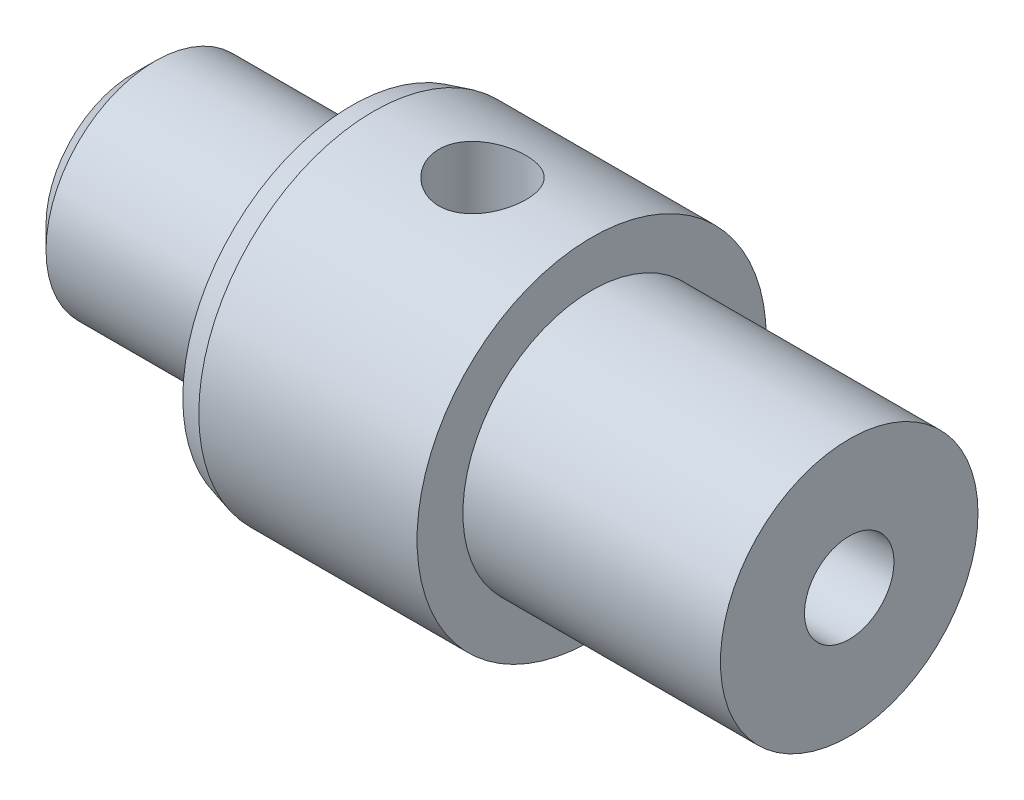
SolidWorks part; units mm, degrees
ref_plane "Front Plane" through (0, 0, 0) normal (0, 0, 1) x (1, 0, 0)
ref_plane "Top Plane" through (0, 0, 0) normal (0, 1, 0) x (1, 0, 0)
ref_plane "Right Plane" through (0, 0, 0) normal (1, 0, 0) x (0, 0, -1)
sketch "Sketch1" plane through (0, 0, 0) normal (0, 0, 1) x (1, 0, 0)
  line L0 (5, 4) -> (5, 0)
  line L1 (5, 0) -> (10.5, 0)
  line L2 (10.5, 0) -> (10.5, 4)
  line L3 (10.5, 4) -> (5, 4)
  line L4 (5, 0) -> (10.5, 0) construction
revolve "Revolve1" add sketch "Sketch1" angle 360 about L4
sketch "Sketch2" plane through (5, 0, 0) normal (-1, 0, 0) x (0, 0, 1)
  circle A0 centre (0, 0) radius 2.5
extrude "Boss-Extrude1" add sketch "Sketch2" along normal blind 5
sketch "Sketch3" plane through (10.5, 0, 0) normal (1, 0, 0) x (0, 0, -1)
  circle A0 centre (0, 0) radius 2.95
extrude "Boss-Extrude2" add sketch "Sketch3" along normal blind 5.9
hole_wizard "Ø2.0 (2) Diameter Hole1" positions "3DSketch1" profile "Sketch4" hole size "Ø2.0" standard "ANSI Metric"
sketch3d "3DSketch1"
  point P0 (8, -4, 0)
sketch "Sketch4" plane through (8, -4, 0) normal (1, 0, 0) x (0, 0, -1)
  line L0 (0, 0) -> (0, 8)
  line L1 (0, 8) -> (1, 8)
  line L2 (1, 8) -> (1, 0)
  line L5 (1, 0) -> (0, 0)
  line L11 (0, -6.35) -> (0, 107.95) construction
  dimension "Thru Hole Dia." = 2
  dimension "Thru Hole Depth" = 8
hole_wizard "Tap Drill for M2.5x0.45 Tap1" positions "Sketch6" profile "Sketch5" hole size "M2.5x0.45" standard "ANSI Metric"
sketch "Sketch6" plane through (16.4, 0, 0) normal (1, 0, 0) x (0, 0, -1)
  point P0 (0, 0)
sketch "Sketch5" plane through (16.4, 0, 0) normal (0, 1, 0) x (0, 0, -1)
  line L0 (0, 0) -> (0, 6.6159)
  line L1 (0, 6.6159) -> (1.025, 6)
  line L2 (1.025, 6) -> (1.025, 0)
  line L5 (1.025, 0) -> (0, 0)
  line L10 (0, 6.6159) -> (-1.025, 6) construction
  line L11 (0, -6.35) -> (0, 107.95) construction
  dimension "Hole Dia." = 2.05
  dimension "Hole Depth" = 6
  dimension "Drill Angle" = 118
chamfer "Chamfer1" distance 0.5 angle 45 1 edges at (0, 0, 2.5)
chamfer "Chamfer2" distance 0.134 angle 75 1 edges at (5, 0, -4)
